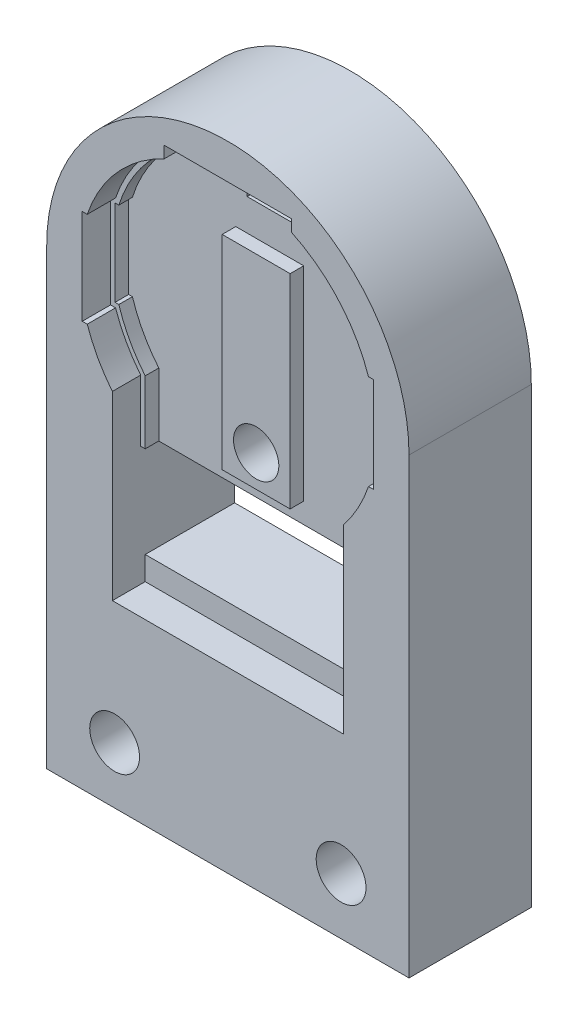
SolidWorks part; units mm, degrees
material "PET"
ref_plane "Front" through (0, 0, 0) normal (0, 0, 1) x (1, 0, 0)
ref_plane "Top" through (0, 0, 0) normal (0, 1, 0) x (1, 0, 0)
ref_plane "Right" through (0, 0, 0) normal (1, 0, 0) x (0, 0, -1)
sketch "Sketch2" plane through (0, 0, 0) normal (0, 0, 1) x (1, 0, 0)
  point P0 (0, 0)
  point P20 (-6.35, -9.4973)
  line B0 (-6.35, -3.0457) -> (6.35, -3.0457)
  line B1 (6.35, -3.0457) -> (6.35, 0.581)
  line B2 (7.7944, 3.2258) -> (8.0391, 3.2258)
  line B3 (8.0391, 3.2258) -> (8.0391, 8.3058)
  line B4 (8.0391, 8.3058) -> (7.7944, 8.3058)
  line B5 (3.4417, 13.2062) -> (3.4417, 13.8199)
  line B6 (3.4417, 13.8199) -> (-3.4417, 13.8199)
  line B7 (-3.4417, 13.8199) -> (-3.4417, 13.2062)
  line B8 (-7.7944, 8.3058) -> (-8.0391, 8.3058)
  line B9 (-8.0391, 8.3058) -> (-8.0391, 3.2258)
  line B10 (-8.0391, 3.2258) -> (-7.7944, 3.2258)
  line B11 (-6.35, 0.581) -> (-6.35, -3.0457)
  line B12 (-5.588, -3.8077) -> (-1.2065, -3.8077)
  line B13 (-1.2065, -3.8077) -> (-1.2065, -3.0457)
  line B14 (-1.2065, -3.0457) -> (-6.35, -3.0457)
  line B15 (-6.35, -3.0457) -> (-6.35, -8.0495)
  line B16 (-6.35, -8.0495) -> (6.35, -8.0495)
  line B17 (6.35, -8.0495) -> (6.35, -3.0457)
  line B18 (6.35, -3.0457) -> (1.2065, -3.0457)
  line B19 (1.2065, -3.0457) -> (1.2065, -3.8077)
  line B20 (1.2065, -3.8077) -> (5.588, -3.8077)
  line B21 (5.588, -3.8077) -> (5.588, -7.2875)
  line B22 (5.588, -7.2875) -> (-5.588, -7.2875)
  line B23 (-5.588, -7.2875) -> (-5.588, -3.8077)
  line B24 (6.35, -8.0495) -> (-6.35, -8.0495)
  line B25 (-6.35, -8.0495) -> (-6.35, -9.4973)
  line B26 (-6.35, -9.4973) -> (6.35, -9.4973)
  line B27 (6.35, -9.4973) -> (6.35, -8.0495)
  circle B28 centre (0, 0) radius 1.27
  arc B29 (6.35, 0.581) -> (7.7944, 3.2258) centre (0, 5.7658) ccw
  arc B30 (7.7944, 8.3058) -> (3.4417, 13.2062) centre (0, 5.7658) ccw
  arc B31 (-3.4417, 13.2062) -> (-7.7944, 8.3058) centre (0, 5.7658) ccw
  arc B32 (-7.7944, 3.2258) -> (-6.35, 0.581) centre (0, 5.7658) ccw
sketch_block_instance "Block1-1"
sketch_block "Block1"
sketch "Sketch1" plane through (0, 0, 0) normal (0, 0, 1) x (1, 0, 0)
  line L71 (-10.16, 5.7658) -> (-10.16, -12.7)
  line L72 (10.16, 5.7658) -> (10.16, -12.7)
  line L80 (-8.1661, 3.0988) -> (-7.8861, 3.0988)
  line L81 (-8.1661, 8.4328) -> (-8.1661, 3.0988)
  line L82 (-7.8861, 8.4328) -> (-8.1661, 8.4328)
  line L83 (-3.5687, 13.9469) -> (-3.5687, 13.2869)
  line L84 (7.8861, 3.0988) -> (8.1661, 3.0988)
  line L85 (8.1661, 3.0988) -> (8.1661, 8.4328)
  line L86 (8.1661, 8.4328) -> (7.8861, 8.4328)
  line L87 (3.5687, 13.2869) -> (3.5687, 13.9469)
  line L88 (3.5687, 13.9469) -> (-3.5687, 13.9469)
  line L90 (-8.1661, 8.4328) -> (-8.1661, 3.0988)
  line L91 (-7.8861, 8.4328) -> (-8.1661, 8.4328)
  line L92 (-3.5687, 13.9469) -> (-3.5687, 13.2869)
  line L94 (8.1661, 3.0988) -> (8.1661, 8.4328)
  line L95 (8.1661, 8.4328) -> (7.8861, 8.4328)
  line L96 (3.5687, 13.2869) -> (3.5687, 13.9469)
  line L97 (3.5687, 13.9469) -> (-3.5687, 13.9469)
  line L111 (-6.477, -9.6243) -> (6.477, -9.6243)
  line L112 (-6.35, -9.4973) -> (6.35, -9.4973) construction
  line L113 (-10.16, -12.7) -> (10.16, -12.7)
  line L116 (-6.477, -3.1727) -> (6.477, -3.1727)
  line L117 (7.8861, 3.0988) -> (8.0391, 3.0988)
  line L118 (6.477, -3.1727) -> (6.477, 0.5359)
  line L119 (-6.477, 0.5359) -> (-6.477, -3.1727)
  line L120 (-8.0391, 3.0988) -> (-7.8861, 3.0988)
  line L122 (7.8861, 3.0988) -> (8.1661, 3.0988)
  line L123 (6.477, -9.6243) -> (6.477, 0.5359)
  line L124 (-6.477, 0.5359) -> (-6.477, -9.6243)
  line L125 (-8.1661, 3.0988) -> (-7.8861, 3.0988)
  circle A0 centre (0, 0) radius 1.27 construction
  circle A1 centre (0, 5.7658) radius 10.16 construction
  arc A26 (-10.16, 5.7658) -> (10.16, 5.7658) centre (0, 5.7658) cw
  arc A30 (-7.8861, 3.0988) -> (-6.4484, 0.5007) centre (0, 5.7658) ccw
  arc A31 (-3.5687, 13.2869) -> (-7.8861, 8.4328) centre (0, 5.7658) ccw
  arc A32 (6.4484, 0.5007) -> (7.8861, 3.0988) centre (0, 5.7658) ccw
  arc A33 (7.8861, 8.4328) -> (3.5687, 13.2869) centre (0, 5.7658) ccw
  arc A35 (-3.5687, 13.2869) -> (-7.8861, 8.4328) centre (0, 5.7658) ccw
  arc A37 (7.8861, 8.4328) -> (3.5687, 13.2869) centre (0, 5.7658) ccw
  arc A44 (6.477, 0.5359) -> (7.8861, 3.0988) centre (0, 5.7658) ccw
  arc A45 (-7.8861, 3.0988) -> (-6.477, 0.5359) centre (0, 5.7658) ccw
  arc A46 (6.477, 0.5359) -> (7.8861, 3.0988) centre (0, 5.7658) ccw
  arc A47 (-7.8861, 3.0988) -> (-6.477, 0.5359) centre (0, 5.7658) ccw
  point P13 (-8.1407, 3.0988)
  point P15 (8.1536, 3.0988)
  dimension "D1" = 2.54
  dimension "D2" = 20.32
  dimension "D4" = 0.127
  dimension "D6" = 12.7
  dimension "D3" = 0.127
  dimension "D5" = 0.127
extrude "Boss-Extrude1" add sketch "Sketch1" along normal blind 1.5875
sketch "Sketch3" plane through (0, 0, 0) normal (0, 0, -1) x (-1, 0, 0)
  line L0 (-6.477, -2.9187) -> (-6.223, -2.9187)
  line L1 (-6.477, -9.6243) -> (-6.477, 0.5359) construction
  line L2 (6.223, -2.9187) -> (6.477, -2.9187)
  line L3 (6.477, 0.5359) -> (6.477, -9.6243) construction
  line L4 (6.35, -3.0457) -> (-6.35, -3.0457) construction
  line L5 (-6.477, -2.9187) -> (-6.477, -9.6243)
  line L6 (-6.477, -9.6243) -> (6.477, -9.6243)
  line L7 (6.477, -9.6243) -> (6.477, -2.9187)
  line L8 (0, 0) -> (0, -1.7757) construction
  line L9 (-1.905, 9.6543) -> (1.905, 9.6543)
  line L10 (-1.905, 9.6543) -> (-1.905, -1.7757)
  line L11 (-1.905, -1.7757) -> (1.905, -1.7757)
  line L12 (1.905, 9.6543) -> (1.905, -1.7757)
  line L99 (10.16, -12.7) -> (-10.16, -12.7) construction
  line L100 (10.16, 5.7658) -> (10.16, -12.7) construction
  line L101 (-10.16, -12.7) -> (-10.16, 5.7658) construction
  line L102 (10.16, -12.7) -> (-10.16, -12.7)
  line L103 (10.16, 5.7658) -> (10.16, -12.7)
  line L104 (-10.16, -12.7) -> (-10.16, 5.7658)
  line L107 (-6.223, -9.6243) -> (-6.223, 0.5359)
  line L108 (-6.223, -2.9187) -> (-6.223, 0.6265)
  line L111 (-7.9121, 3.3528) -> (-7.7017, 3.3528)
  line L112 (-7.9121, 8.1788) -> (-7.9121, 3.3528)
  line L113 (-7.7017, 8.1788) -> (-7.9121, 8.1788)
  line L114 (-3.3147, 13.6929) -> (-3.3147, 13.1246)
  line L115 (3.3147, 13.6929) -> (-3.3147, 13.6929)
  line L116 (3.3147, 13.1246) -> (3.3147, 13.6929)
  line L117 (7.9121, 8.1788) -> (7.7017, 8.1788)
  line L118 (7.9121, 3.3528) -> (7.9121, 8.1788)
  line L119 (7.7017, 3.3528) -> (7.9121, 3.3528)
  line L120 (6.223, -9.3703) -> (6.223, 0.6265)
  line L121 (-6.223, -9.3703) -> (6.223, -9.3703)
  line L122 (-6.223, 0.6265) -> (-6.223, -9.3703)
  line L123 (-7.9121, 3.3528) -> (-7.7017, 3.3528)
  line L124 (-7.9121, 8.1788) -> (-7.9121, 3.3528)
  line L125 (-7.7017, 8.1788) -> (-7.9121, 8.1788)
  line L126 (-3.3147, 13.6929) -> (-3.3147, 13.1246)
  line L127 (3.3147, 13.6929) -> (-3.3147, 13.6929)
  line L128 (3.3147, 13.1246) -> (3.3147, 13.6929)
  line L129 (7.9121, 8.1788) -> (7.7017, 8.1788)
  line L130 (7.9121, 3.3528) -> (7.9121, 8.1788)
  line L131 (7.7017, 3.3528) -> (7.9121, 3.3528)
  line L132 (6.223, -2.9187) -> (6.223, 0.6265)
  arc A41 (10.16, 5.7658) -> (-10.16, 5.7658) centre (0, 5.7658) ccw construction
  arc A42 (10.16, 5.7658) -> (-10.16, 5.7658) centre (0, 5.7658) ccw
  arc A45 (-3.3147, 13.1246) -> (-7.7017, 8.1788) centre (0, 5.7658) ccw
  arc A46 (7.7017, 8.1788) -> (3.3147, 13.1246) centre (0, 5.7658) ccw
  arc A47 (6.223, 0.6265) -> (7.7017, 3.3528) centre (0, 5.7658) ccw
  arc A48 (-7.7017, 3.3528) -> (-6.223, 0.6265) centre (0, 5.7658) ccw
  arc A49 (-3.3147, 13.1246) -> (-7.7017, 8.1788) centre (0, 5.7658) ccw
  arc A50 (7.7017, 8.1788) -> (3.3147, 13.1246) centre (0, 5.7658) ccw
  arc A51 (6.223, 0.6265) -> (7.7017, 3.3528) centre (0, 5.7658) ccw
  arc A52 (-7.7017, 3.3528) -> (-6.223, 0.6265) centre (0, 5.7658) ccw
  point P27 (1.905, -1.3214)
  dimension "D3" = 0.127
  dimension "D4" = 0.127
  dimension "D5" = 11.43
  dimension "D6" = 3.81
  dimension "D7" = 1.27
  dimension "D1" = 0.254
  dimension "D2" = 0.254
extrude "Boss-Extrude2" add sketch "Sketch3" along normal blind 0.762
sketch "Sketch4" plane through (0, 0, -0.762) normal (0, 0, -1) x (-1, 0, 0)
  line L0 (6.477, -2.9187) -> (6.477, -9.6243) construction
  line L1 (-6.477, -9.6243) -> (6.477, -9.6243)
  line L2 (-6.477, -9.6243) -> (-6.477, -8.3035)
  line L3 (-6.477, -8.3035) -> (6.477, -8.3035)
  line L4 (6.477, -9.6243) -> (6.477, -8.3035)
  line L5 (6.35, -8.0495) -> (-6.35, -8.0495) construction
  dimension "D1" = 0.254
extrude "Boss-Extrude3" add sketch "Sketch4" against normal blind 0.508
sketch "Sketch5" plane through (0, 0, -0.762) normal (0, 0, -1) x (-1, 0, 0)
  line L0 (6.477, -2.9187) -> (6.477, -8.3035) construction
  line L1 (6.477, -2.9187) -> (-6.477, -2.9187)
  line L2 (6.477, -2.9187) -> (6.477, -8.3035)
  line L3 (10.16, -12.7) -> (10.16, 5.7658)
  line L4 (-10.16, 5.7658) -> (-10.16, -12.7)
  line L5 (-10.16, -12.7) -> (10.16, -12.7)
  line L6 (10.16, -12.7) -> (10.16, 5.7658)
  line L7 (-10.16, 5.7658) -> (-10.16, -12.7)
  line L8 (-10.16, -12.7) -> (10.16, -12.7)
  line L9 (6.477, -8.3035) -> (-6.477, -8.3035)
  line L10 (-6.477, -2.9187) -> (-6.477, -8.3035)
  line L11 (6.35, -3.0457) -> (-6.35, -3.0457) construction
  arc A1 (10.16, 5.7658) -> (-10.16, 5.7658) centre (0, 5.7658) ccw
  arc A2 (10.16, 5.7658) -> (-10.16, 5.7658) centre (0, 5.7658) ccw
  dimension "D2" = 0.127
  dimension "D1" = 0
extrude "Boss-Extrude4" add sketch "Sketch5" along normal offset from surface (4.5085 mm away) 6.858 up to face at (0, -0.9271, 1.5875)
extrude "Cut-Extrude1" cut sketch "Sketch2" against normal through all both and the other way through all contours B28
sketch "Sketch6" plane through (0, 0, -5.2705) normal (0, 0, -1) x (-1, 0, 0)
  line L1 (1.3931, 2.413) -> (-1.3931, 2.413)
  line L2 (-1.3931, 2.413) -> (-2.7863, 0)
  line L3 (-2.7863, 0) -> (-1.3931, -2.413)
  line L4 (-1.3931, -2.413) -> (1.3931, -2.413)
  line L5 (1.3931, -2.413) -> (2.7863, 0)
  line L6 (2.7863, 0) -> (1.3931, 2.413)
  circle A0 centre (0, 0) radius 2.413 construction
  dimension "D1" = 4.826
extrude "Cut-Extrude2" cut sketch "Sketch6" against normal blind 1.905
sketch "Sketch7" plane through (0, 0, -5.2705) normal (0, 0, -1) x (-1, 0, 0)
  line L1 (-10.16, -12.7) -> (10.16, -12.7)
  line L2 (-10.16, -12.7) -> (-10.16, -19.6342)
  line L3 (-10.16, -19.6342) -> (10.16, -19.6342)
  line L4 (10.16, -12.7) -> (10.16, -19.6342)
  point P5 (10.16, -12.7)
  dimension "D1" = 6.9342
extrude "Boss-Extrude5" add sketch "Sketch7" against normal up to surface (6.858 mm away) up to face at (0, -0.9271, 1.5875)
sketch "Sketch8" plane through (0, 0, -5.2705) normal (0, 0, -1) x (-1, 0, 0)
  line L0 (-10.16, -13.2842) -> (10.16, -13.2842) construction
  line L1 (-10.16, 5.7658) -> (-10.16, -19.6342) construction
  line L2 (10.16, -19.6342) -> (10.16, 5.7658) construction
  line L3 (-10.16, -19.6342) -> (10.16, -19.6342) construction
  line L4 (-6.35, -16.4592) -> (6.35, -16.4592) construction
  line L5 (0, -16.4592) -> (0, -13.2842) construction
  circle A0 centre (-6.35, -16.4592) radius 1.397
  circle A1 centre (6.35, -16.4592) radius 1.397
  dimension "D1" = 2.794
  dimension "D2" = 6.35
  dimension "D3" = 3.175
  dimension "D4" = 12.7
extrude "Cut-Extrude3" cut sketch "Sketch8" against normal through all
sketch "Sketch9" plane through (0, 0, -5.2705) normal (0, 0, -1) x (-1, 0, 0)
  line L0 (0, 0) -> (0, 11.43) construction
  line L1 (-1.27, 12.7) -> (1.27, 12.7)
  line L2 (-1.27, 12.7) -> (-1.27, 11.43)
  line L3 (-1.27, 11.43) -> (1.27, 11.43)
  line L4 (1.27, 12.7) -> (1.27, 11.43)
  dimension "D1" = 1.27
  dimension "D2" = 2.54
  dimension "D3" = 11.43
extrude "Cut-Extrude4" cut sketch "Sketch9" against normal through all contours L1 L4 L3 L2
